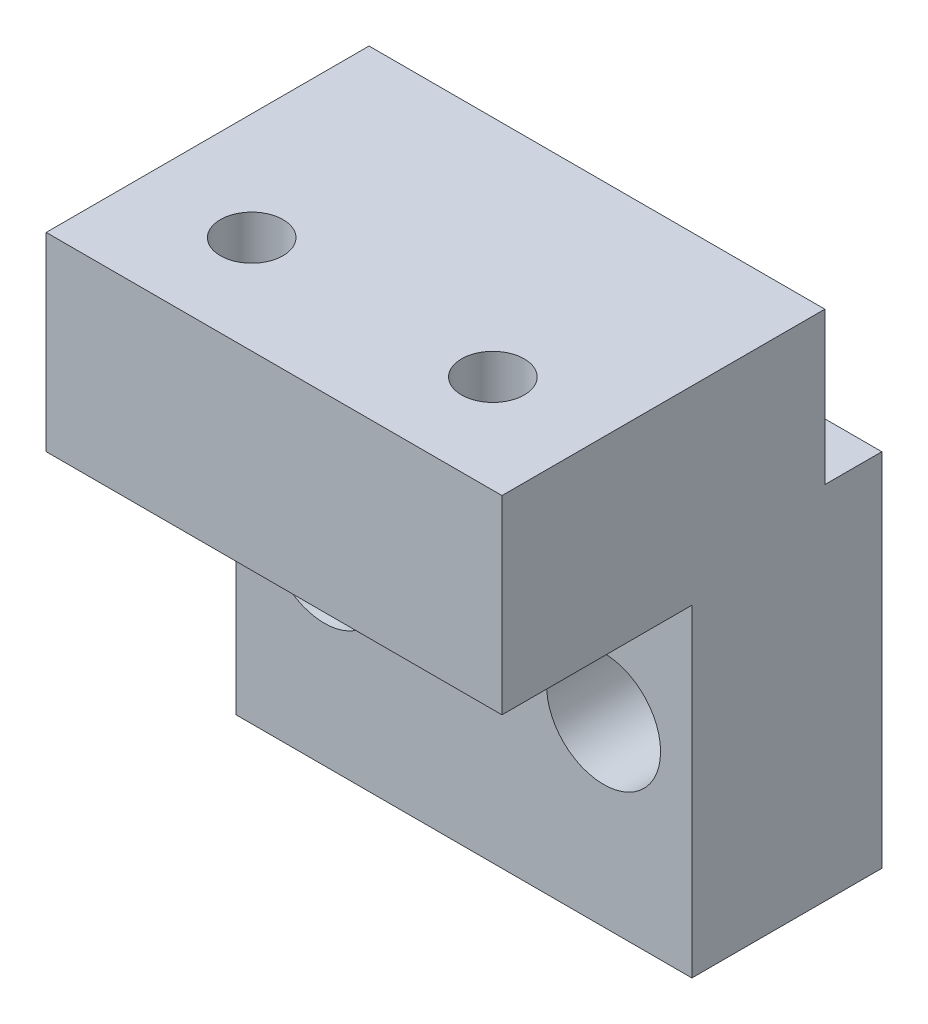
SolidWorks part; units mm, degrees
ref_plane "Front Plane" through (0, 0, 0) normal (0, 0, 1) x (1, 0, 0)
ref_plane "Top Plane" through (0, 0, 0) normal (0, 1, 0) x (1, 0, 0)
ref_plane "Right Plane" through (0, 0, 0) normal (1, 0, 0) x (0, 0, -1)
sketch "Sketch1" plane through (0, 0, 0) normal (0, 0, 1) x (1, 0, 0)
  line L1 (-24, 47) -> (0, 47)
  line L2 (-24, 47) -> (-24, 28)
  line L3 (-24, 28) -> (0, 28)
  line L4 (0, 47) -> (0, 28)
  circle A0 centre (-19.35, 37.5) radius 1.65
  circle A1 centre (-4.65, 37.5) radius 1.65
  circle A2 centre (-19.35, 37.5) radius 1.65 construction
extrude "Boss-Extrude1" add sketch "Sketch1" along normal blind 10
sketch "Sketch2" plane through (0, 0, 10) normal (0, 0, 1) x (1, 0, 0)
  circle A0 centre (-4.65, 37.5) radius 3
  circle A1 centre (-19.35, 37.5) radius 3
  dimension "D1" = 6
extrude "Cut-Extrude1" cut sketch "Sketch2" against normal blind 5.5
sketch "Sketch3" plane through (0, 0, 10) normal (0, 0, 1) x (1, 0, 0)
  line L0 (-1060.3236, 56) -> (48939.6764, 56) construction
  circle A0 centre (-180.0069, 67) radius 11 construction
sketch "Sketch4" plane through (0, 47, 0) normal (0, 1, 0) x (1, 0, 0)
  line L0 (-24, -10) -> (-24, 0) construction
  line L1 (0, -10) -> (-24, -10)
  line L2 (0, -10) -> (0, -3)
  line L3 (0, -3) -> (-24, -3)
  line L4 (-24, -10) -> (-24, -3)
  line L5 (0, 0) -> (-24, 0) construction
  dimension "D1" = 3
extrude "Boss-Extrude2" add sketch "Sketch4" along normal blind 8
sketch "Sketch5" plane through (0, 55, 0) normal (0, 1, 0) x (1, 0, 0)
  line L0 (-1067.7804, -9) -> (48932.2196, -9) construction
  line L1 (-1066.6547, -2) -> (48933.3453, -2) construction
  line L2 (-191.0069, -9) -> (-169.0069, -9) construction
  line L3 (-169.0069, -2) -> (-191.0069, -2) construction
sketch "Sketch6" plane through (0, 0, 10) normal (0, 0, 1) x (1, 0, 0)
  line L0 (0, 28) -> (0, 55) construction
  line L1 (0, 45) -> (-24, 45)
  line L2 (0, 45) -> (0, 55)
  line L3 (0, 55) -> (-24, 55)
  line L4 (-24, 45) -> (-24, 55)
  dimension "D1" = 10
extrude "Boss-Extrude3" add sketch "Sketch6" along normal blind 10
sketch "Sketch7" plane through (0, 55, 0) normal (0, 1, 0) x (1, 0, 0)
  line L0 (-12, -1018) -> (-12, 48982) construction
  line L1 (0, -20) -> (-24, -20) construction
  line L2 (0, -20) -> (0, -3) construction
  circle A0 centre (-5.65, -14.8295) radius 1.65
  circle A1 centre (-18.35, -14.8295) radius 1.65
  point P9 (-12, -20)
  dimension "D1" = 3.3
  dimension "D2" = 4
extrude "Cut-Extrude2" cut sketch "Sketch7" against normal through all
sketch "Sketch8" plane through (0, 45, 0) normal (0, -1, 0) x (1, 0, 0)
  line L1 (-2.3591, 14.8295) -> (-4.0046, 17.6795)
  line L2 (-4.0046, 17.6795) -> (-7.2954, 17.6795)
  line L3 (-7.2954, 17.6795) -> (-8.9409, 14.8295)
  line L4 (-8.9409, 14.8295) -> (-7.2954, 11.9795)
  line L5 (-7.2954, 11.9795) -> (-4.0046, 11.9795)
  line L6 (-4.0046, 11.9795) -> (-2.3591, 14.8295)
  line L7 (-15.0591, 14.8295) -> (-16.7046, 17.6795)
  line L8 (-16.7046, 17.6795) -> (-19.9954, 17.6795)
  line L9 (-19.9954, 17.6795) -> (-21.6409, 14.8295)
  line L10 (-21.6409, 14.8295) -> (-19.9954, 11.9795)
  line L11 (-19.9954, 11.9795) -> (-16.7046, 11.9795)
  line L12 (-16.7046, 11.9795) -> (-15.0591, 14.8295)
  circle A0 centre (-5.65, 14.8295) radius 2.85 construction
  circle A1 centre (-18.35, 14.8295) radius 2.85 construction
  dimension "D1" = 5.7
extrude "Cut-Extrude3" cut sketch "Sketch8" against normal blind 2.2
